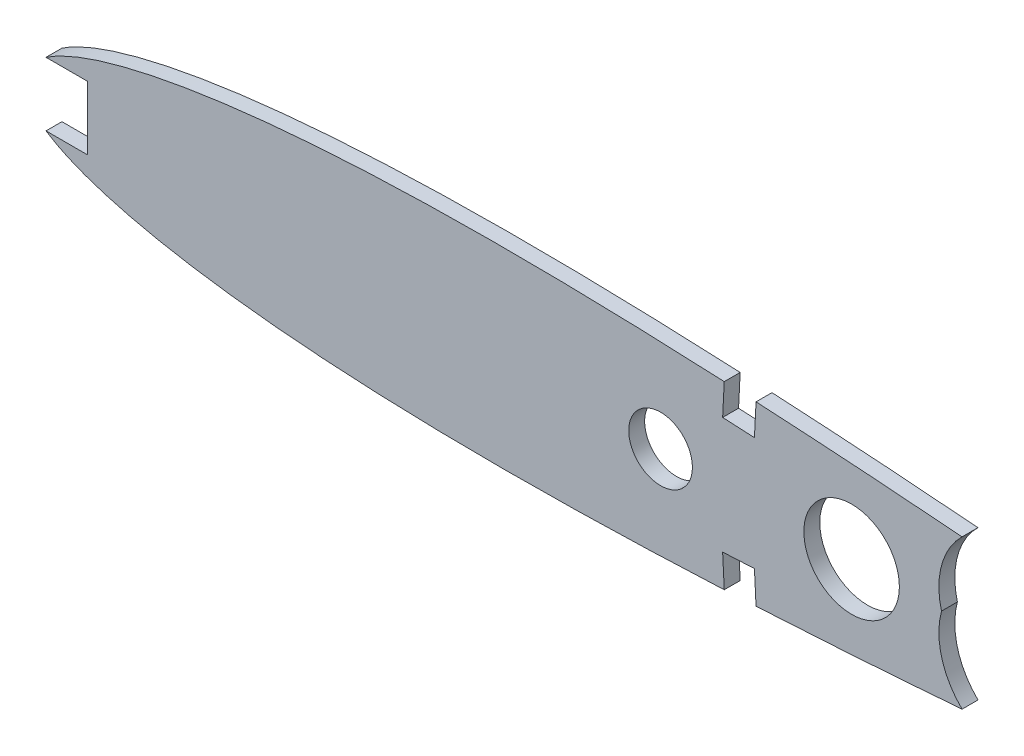
SolidWorks part; units mm, degrees
material "Plywood"
ref_plane "Front Plane" through (0, 0, 0) normal (0, 0, 1) x (1, 0, 0)
ref_plane "Top Plane" through (0, 0, 0) normal (0, 1, 0) x (1, 0, 0)
ref_plane "Right Plane" through (0, 0, 0) normal (1, 0, 0) x (0, 0, -1)
curve "Curve1"
  spline degree 3 poles (318.9616, -0.5388, 0) (318.9616, 0.5388, 0) (317.8871, 0.4072, 0) (316.5257, 0.7904, 0) (314.029, 1.0273, 0) (310.6656, 1.5357, 0) (306.333, 2.103, 0) (301.1081, 2.8022, 0) (295.0047, 3.5926, 0) (288.0667, 4.4725, 0) (280.3349, 5.4267, 0) (271.8575, 6.4421, 0) (262.6867, 7.5062, 0) (252.8789, 8.6045, 0) (242.4947, 9.7236, 0) (231.5982, 10.8496, 0) (220.2564, 11.9679, 0) (208.5394, 13.0629, 0) (196.5193, 14.1202, 0) (184.2704, 15.122, 0) (171.8679, 16.0521, 0) (159.3884, 16.8933, 0) (146.9087, 17.6278, 0) (134.5058, 18.2372, 0) (122.2562, 18.7052, 0) (110.2351, 19.0165, 0) (98.5168, 19.156, 0) (87.1732, 19.1125, 0) (76.2743, 18.8777, 0) (65.8873, 18.4456, 0) (56.076, 17.8151, 0) (46.9007, 16.9881, 0) (38.4176, 15.971, 0) (30.6784, 14.7725, 0) (23.73, 13.4051, 0) (17.6131, 11.8842, 0) (12.3624, 10.2248, 0) (8.0047, 8.4423, 0) (4.5539, 6.5486, 0) (2.0152, 4.5401, 0) (0.3892, 2.3682, 0) (-0.1814, 0, 0) (0.3892, -2.3682, 0) (2.0152, -4.5401, 0) (4.5539, -6.5486, 0) (8.0047, -8.4423, 0) (12.3624, -10.2248, 0) (17.6131, -11.8842, 0) (23.73, -13.4051, 0) (30.6784, -14.7725, 0) (38.4176, -15.971, 0) (46.9007, -16.9881, 0) (56.076, -17.8151, 0) (65.8873, -18.4456, 0) (76.2743, -18.8777, 0) (87.1732, -19.1125, 0) (98.5168, -19.156, 0) (110.2351, -19.0165, 0) (122.2562, -18.7052, 0) (134.5058, -18.2372, 0) (146.9087, -17.6278, 0) (159.3884, -16.8933, 0) (171.8679, -16.0521, 0) (184.2704, -15.122, 0) (196.5193, -14.1202, 0) (208.5394, -13.0629, 0) (220.2564, -11.9679, 0) (231.5982, -10.8496, 0) (242.4947, -9.7236, 0) (252.8789, -8.6045, 0) (262.6867, -7.5062, 0) (271.8575, -6.4421, 0) (280.3349, -5.4267, 0) (288.0667, -4.4725, 0) (295.0047, -3.5926, 0) (301.1081, -2.8022, 0) (306.333, -2.103, 0) (310.6656, -1.5357, 0) (314.029, -1.0273, 0) (316.5257, -0.7904, 0) (317.8871, -0.4072, 0) (318.9616, -0.5388, 0) (318.9616, 0.5388, 0) (317.8871, 0.4072, 0) knots -0.004279 -0.001997 -0.001234 0 0.000762 0.003045 0.006832 0.012101 0.018818 0.026939 0.036415 0.047185 0.05918 0.072328 0.086544 0.101741 0.117823 0.134691 0.15224 0.170361 0.188941 0.207865 0.227016 0.246276 0.265525 0.284645 0.30352 0.322035 0.340078 0.357543 0.374325 0.39033 0.405464 0.419644 0.432793 0.444844 0.455738 0.465429 0.473886 0.481102 0.487102 0.491975 0.495931 0.499383 0.502835 0.50679 0.511664 0.517664 0.524879 0.533337 0.543028 0.553922 0.565972 0.579122 0.593302 0.608436 0.62444 0.641223 0.658687 0.676731 0.695245 0.714121 0.733241 0.75249 0.77175 0.7909 0.809825 0.828404 0.846525 0.864074 0.880942 0.897025 0.912222 0.926438 0.939585 0.951581 0.962351 0.971826 0.979948 0.986664 0.991933 0.995721 0.998003 0.998766 1 1.000762 1.003045 1.006832 periodic
sketch "Sketch2" plane through (0, 0, 0) normal (0, 0, 1) x (1, 0, 0)
  spline S0 degree 3 poles (318.9616, -0.5388) (318.9616, 0.5388) (317.8871, 0.4072) (316.5257, 0.7904) (314.029, 1.0273) (310.6656, 1.5357) (306.333, 2.103) (301.1081, 2.8022) (295.0047, 3.5926) (288.0667, 4.4725) (280.3349, 5.4267) (271.8575, 6.4421) (262.6867, 7.5062) (252.8789, 8.6045) (242.4947, 9.7236) (231.5982, 10.8496) (220.2564, 11.9679) (208.5394, 13.0629) (196.5193, 14.1202) (184.2704, 15.122) (171.8679, 16.0521) (159.3884, 16.8933) (146.9087, 17.6278) (134.5058, 18.2372) (122.2562, 18.7052) (110.2351, 19.0165) (98.5168, 19.156) (87.1732, 19.1125) (76.2743, 18.8777) (65.8873, 18.4456) (56.076, 17.8151) (46.9007, 16.9881) (38.4176, 15.971) (30.6784, 14.7725) (23.73, 13.4051) (17.6131, 11.8842) (12.3624, 10.2248) (8.0047, 8.4423) (4.5539, 6.5486) (2.0152, 4.5401) (0.3892, 2.3682) (-0.1814, 0) (0.3892, -2.3682) (2.0152, -4.5401) (4.5539, -6.5486) (8.0047, -8.4423) (12.3624, -10.2248) (17.6131, -11.8842) (23.73, -13.4051) (30.6784, -14.7725) (38.4176, -15.971) (46.9007, -16.9881) (56.076, -17.8151) (65.8873, -18.4456) (76.2743, -18.8777) (87.1732, -19.1125) (98.5168, -19.156) (110.2351, -19.0165) (122.2562, -18.7052) (134.5058, -18.2372) (146.9087, -17.6278) (159.3884, -16.8933) (171.8679, -16.0521) (184.2704, -15.122) (196.5193, -14.1202) (208.5394, -13.0629) (220.2564, -11.9679) (231.5982, -10.8496) (242.4947, -9.7236) (252.8789, -8.6045) (262.6867, -7.5062) (271.8575, -6.4421) (280.3349, -5.4267) (288.0667, -4.4725) (295.0047, -3.5926) (301.1081, -2.8022) (306.333, -2.103) (310.6656, -1.5357) (314.029, -1.0273) (316.5257, -0.7904) (317.8871, -0.4072) (318.9616, -0.5388) (318.9616, 0.5388) (317.8871, 0.4072) knots -0.004279 -0.001997 -0.001234 0 0.000762 0.003045 0.006832 0.012101 0.018818 0.026939 0.036415 0.047185 0.05918 0.072328 0.086544 0.101741 0.117823 0.134691 0.15224 0.170361 0.188941 0.207865 0.227016 0.246276 0.265525 0.284645 0.30352 0.322035 0.340078 0.357543 0.374325 0.39033 0.405464 0.419644 0.432793 0.444844 0.455738 0.465429 0.473886 0.481102 0.487102 0.491975 0.495931 0.499383 0.502835 0.50679 0.511664 0.517664 0.524879 0.533337 0.543028 0.553922 0.565972 0.579122 0.593302 0.608436 0.62444 0.641223 0.658687 0.676731 0.695245 0.714121 0.733241 0.75249 0.77175 0.7909 0.809825 0.828404 0.846525 0.864074 0.880942 0.897025 0.912222 0.926438 0.939585 0.951581 0.962351 0.971826 0.979948 0.986664 0.991933 0.995721 0.998003 0.998766 1 1.000762 1.003045 1.006832 only from (318.77, 0.4017) to (318.77, 0.4017) construction
  spline S1 degree 3 poles (318.9616, -0.5388) (318.9616, 0.5388) (317.8871, 0.4072) (316.5257, 0.7904) (314.029, 1.0273) (310.6656, 1.5357) (306.333, 2.103) (301.1081, 2.8022) (295.0047, 3.5926) (288.0667, 4.4725) (280.3349, 5.4267) (271.8575, 6.4421) (262.6867, 7.5062) (252.8789, 8.6045) (242.4947, 9.7236) (231.5982, 10.8496) (220.2564, 11.9679) (208.5394, 13.0629) (196.5193, 14.1202) (184.2704, 15.122) (171.8679, 16.0521) (159.3884, 16.8933) (146.9087, 17.6278) (134.5058, 18.2372) (122.2562, 18.7052) (110.2351, 19.0165) (98.5168, 19.156) (87.1732, 19.1125) (76.2743, 18.8777) (65.8873, 18.4456) (56.076, 17.8151) (46.9007, 16.9881) (38.4176, 15.971) (30.6784, 14.7725) (23.73, 13.4051) (17.6131, 11.8842) (12.3624, 10.2248) (8.0047, 8.4423) (4.5539, 6.5486) (2.0152, 4.5401) (0.3892, 2.3682) (-0.1814, 0) (0.3892, -2.3682) (2.0152, -4.5401) (4.5539, -6.5486) (8.0047, -8.4423) (12.3624, -10.2248) (17.6131, -11.8842) (23.73, -13.4051) (30.6784, -14.7725) (38.4176, -15.971) (46.9007, -16.9881) (56.076, -17.8151) (65.8873, -18.4456) (76.2743, -18.8777) (87.1732, -19.1125) (98.5168, -19.156) (110.2351, -19.0165) (122.2562, -18.7052) (134.5058, -18.2372) (146.9087, -17.6278) (159.3884, -16.8933) (171.8679, -16.0521) (184.2704, -15.122) (196.5193, -14.1202) (208.5394, -13.0629) (220.2564, -11.9679) (231.5982, -10.8496) (242.4947, -9.7236) (252.8789, -8.6045) (262.6867, -7.5062) (271.8575, -6.4421) (280.3349, -5.4267) (288.0667, -4.4725) (295.0047, -3.5926) (301.1081, -2.8022) (306.333, -2.103) (310.6656, -1.5357) (314.029, -1.0273) (316.5257, -0.7904) (317.8871, -0.4072) (318.9616, -0.5388) (318.9616, 0.5388) (317.8871, 0.4072) knots -0.004279 -0.001997 -0.001234 0 0.000762 0.003045 0.006832 0.012101 0.018818 0.026939 0.036415 0.047185 0.05918 0.072328 0.086544 0.101741 0.117823 0.134691 0.15224 0.170361 0.188941 0.207865 0.227016 0.246276 0.265525 0.284645 0.30352 0.322035 0.340078 0.357543 0.374325 0.39033 0.405464 0.419644 0.432793 0.444844 0.455738 0.465429 0.473886 0.481102 0.487102 0.491975 0.495931 0.499383 0.502835 0.50679 0.511664 0.517664 0.524879 0.533337 0.543028 0.553922 0.565972 0.579122 0.593302 0.608436 0.62444 0.641223 0.658687 0.676731 0.695245 0.714121 0.733241 0.75249 0.77175 0.7909 0.809825 0.828404 0.846525 0.864074 0.880942 0.897025 0.912222 0.926438 0.939585 0.951581 0.962351 0.971826 0.979948 0.986664 0.991933 0.995721 0.998003 0.998766 1 1.000762 1.003045 1.006832 only from (318.77, 0.4017) to (318.77, 0.4017)
extrude "Boss-Extrude1" add sketch "Sketch2" along normal blind 3.175
sketch "Sketch3" plane through (0, 0, 3.175) normal (0, 0, 1) x (1, 0, 0)
  line L5 (146.0418, 17.6541) -> (145.7194, 11.3041)
  line L6 (139.7, 17.9761) -> (139.3776, 11.6261)
  line L7 (145.7194, 11.3041) -> (139.3776, 11.6261)
  line L8 (145.7194, -11.3041) -> (139.3776, -11.6261)
  line L9 (145.7194, -11.3041) -> (146.0418, -17.6541)
  line L10 (139.3776, -11.6261) -> (139.7, -17.9761)
  line L13 (139.7, 17.9761) -> (139.9721, 23.3363)
  line L14 (146.0418, 17.6541) -> (146.314, 23.0144)
  line L15 (139.9721, 23.3363) -> (146.314, 23.0144)
  line L17 (139.7, -17.9761) -> (139.8768, -21.459)
  line L18 (146.0418, -17.6541) -> (146.2187, -21.137)
  line L19 (139.8768, -21.459) -> (146.2187, -21.137)
  circle A1 centre (127, 0) radius 6.35
  spline S0 degree 3 poles (318.9616, -0.5388) (318.9616, 0.5388) (317.8871, 0.4072) (316.5257, 0.7904) (314.029, 1.0273) (310.6656, 1.5357) (306.333, 2.103) (301.1081, 2.8022) (295.0047, 3.5926) (288.0667, 4.4725) (280.3349, 5.4267) (271.8575, 6.4421) (262.6867, 7.5062) (252.8789, 8.6045) (242.4947, 9.7236) (231.5982, 10.8496) (220.2564, 11.9679) (208.5394, 13.0629) (196.5193, 14.1202) (184.2704, 15.122) (171.8679, 16.0521) (159.3884, 16.8933) (146.9087, 17.6278) (134.5058, 18.2372) (122.2562, 18.7052) (110.2351, 19.0165) (98.5168, 19.156) (87.1732, 19.1125) (76.2743, 18.8777) (65.8873, 18.4456) (56.076, 17.8151) (46.9007, 16.9881) (38.4176, 15.971) (30.6784, 14.7725) (23.73, 13.4051) (17.6131, 11.8842) (12.3624, 10.2248) (8.0047, 8.4423) (4.5539, 6.5486) (2.0152, 4.5401) (0.3892, 2.3682) (-0.1814, 0) (0.3892, -2.3682) (2.0152, -4.5401) (4.5539, -6.5486) (8.0047, -8.4423) (12.3624, -10.2248) (17.6131, -11.8842) (23.73, -13.4051) (30.6784, -14.7725) (38.4176, -15.971) (46.9007, -16.9881) (56.076, -17.8151) (65.8873, -18.4456) (76.2743, -18.8777) (87.1732, -19.1125) (98.5168, -19.156) (110.2351, -19.0165) (122.2562, -18.7052) (134.5058, -18.2372) (146.9087, -17.6278) (159.3884, -16.8933) (171.8679, -16.0521) (184.2704, -15.122) (196.5193, -14.1202) (208.5394, -13.0629) (220.2564, -11.9679) (231.5982, -10.8496) (242.4947, -9.7236) (252.8789, -8.6045) (262.6867, -7.5062) (271.8575, -6.4421) (280.3349, -5.4267) (288.0667, -4.4725) (295.0047, -3.5926) (301.1081, -2.8022) (306.333, -2.103) (310.6656, -1.5357) (314.029, -1.0273) (316.5257, -0.7904) (317.8871, -0.4072) (318.9616, -0.5388) (318.9616, 0.5388) (317.8871, 0.4072) knots -0.004279 -0.001997 -0.001234 0 0.000762 0.003045 0.006832 0.012101 0.018818 0.026939 0.036415 0.047185 0.05918 0.072328 0.086544 0.101741 0.117823 0.134691 0.15224 0.170361 0.188941 0.207865 0.227016 0.246276 0.265525 0.284645 0.30352 0.322035 0.340078 0.357543 0.374325 0.39033 0.405464 0.419644 0.432793 0.444844 0.455738 0.465429 0.473886 0.481102 0.487102 0.491975 0.495931 0.499383 0.502835 0.50679 0.511664 0.517664 0.524879 0.533337 0.543028 0.553922 0.565972 0.579122 0.593302 0.608436 0.62444 0.641223 0.658687 0.676731 0.695245 0.714121 0.733241 0.75249 0.77175 0.7909 0.809825 0.828404 0.846525 0.864074 0.880942 0.897025 0.912222 0.926438 0.939585 0.951581 0.962351 0.971826 0.979948 0.986664 0.991933 0.995721 0.998003 0.998766 1 1.000762 1.003045 1.006832 only from (318.77, 0.4017) to (318.77, 0.4017) construction
  dimension "D1" = 6.35
  dimension "D2" = 12.7
  dimension "D3" = 6.35
  dimension "D4" = 127
  dimension "D5" = 12.7
  dimension "D6" = 0
  dimension "D7" = 6.35
  dimension "D8" = 6.35
extrude "Cut-Extrude1" cut sketch "Sketch3" against normal through all
sketch "Sketch4" plane through (0, 0, 3.175) normal (0, 0, 1) x (1, 0, 0)
  line L5 (12.7, 6.35) -> (12.7, -6.35)
  line L6 (12.7, 6.35) -> (0, 6.35)
  line L7 (12.7, -6.35) -> (0, -6.35)
  line L8 (0, 6.35) -> (0, -6.35)
  line L9 (12.7, 6.35) -> (0, -6.35) construction
  line L10 (12.7, -6.35) -> (0, 6.35) construction
  spline S0 degree 3 poles (318.9616, -0.5388) (318.9616, 0.5388) (317.8871, 0.4072) (316.5257, 0.7904) (314.029, 1.0273) (310.6656, 1.5357) (306.333, 2.103) (301.1081, 2.8022) (295.0047, 3.5926) (288.0667, 4.4725) (280.3349, 5.4267) (271.8575, 6.4421) (262.6867, 7.5062) (252.8789, 8.6045) (242.4947, 9.7236) (231.5982, 10.8496) (220.2564, 11.9679) (208.5394, 13.0629) (196.5193, 14.1202) (184.2704, 15.122) (171.8679, 16.0521) (159.3884, 16.8933) (146.9087, 17.6278) (134.5058, 18.2372) (122.2562, 18.7052) (110.2351, 19.0165) (98.5168, 19.156) (87.1732, 19.1125) (76.2743, 18.8777) (65.8873, 18.4456) (56.076, 17.8151) (46.9007, 16.9881) (38.4176, 15.971) (30.6784, 14.7725) (23.73, 13.4051) (17.6131, 11.8842) (12.3624, 10.2248) (8.0047, 8.4423) (4.5539, 6.5486) (2.0152, 4.5401) (0.3892, 2.3682) (-0.1814, 0) (0.3892, -2.3682) (2.0152, -4.5401) (4.5539, -6.5486) (8.0047, -8.4423) (12.3624, -10.2248) (17.6131, -11.8842) (23.73, -13.4051) (30.6784, -14.7725) (38.4176, -15.971) (46.9007, -16.9881) (56.076, -17.8151) (65.8873, -18.4456) (76.2743, -18.8777) (87.1732, -19.1125) (98.5168, -19.156) (110.2351, -19.0165) (122.2562, -18.7052) (134.5058, -18.2372) (146.9087, -17.6278) (159.3884, -16.8933) (171.8679, -16.0521) (184.2704, -15.122) (196.5193, -14.1202) (208.5394, -13.0629) (220.2564, -11.9679) (231.5982, -10.8496) (242.4947, -9.7236) (252.8789, -8.6045) (262.6867, -7.5062) (271.8575, -6.4421) (280.3349, -5.4267) (288.0667, -4.4725) (295.0047, -3.5926) (301.1081, -2.8022) (306.333, -2.103) (310.6656, -1.5357) (314.029, -1.0273) (316.5257, -0.7904) (317.8871, -0.4072) (318.9616, -0.5388) (318.9616, 0.5388) (317.8871, 0.4072) knots -0.004279 -0.001997 -0.001234 0 0.000762 0.003045 0.006832 0.012101 0.018818 0.026939 0.036415 0.047185 0.05918 0.072328 0.086544 0.101741 0.117823 0.134691 0.15224 0.170361 0.188941 0.207865 0.227016 0.246276 0.265525 0.284645 0.30352 0.322035 0.340078 0.357543 0.374325 0.39033 0.405464 0.419644 0.432793 0.444844 0.455738 0.465429 0.473886 0.481102 0.487102 0.491975 0.495931 0.499383 0.502835 0.50679 0.511664 0.517664 0.524879 0.533337 0.543028 0.553922 0.565972 0.579122 0.593302 0.608436 0.62444 0.641223 0.658687 0.676731 0.695245 0.714121 0.733241 0.75249 0.77175 0.7909 0.809825 0.828404 0.846525 0.864074 0.880942 0.897025 0.912222 0.926438 0.939585 0.951581 0.962351 0.971826 0.979948 0.986664 0.991933 0.995721 0.998003 0.998766 1 1.000762 1.003045 1.006832 only from (318.77, 0.4017) to (318.77, 0.4017) construction
  spline S1 degree 3 poles (44.4469, 16.6766) (42.3575, 16.4398) (37.6765, 15.8562) (30.6784, 14.7725) (23.73, 13.4051) (17.6131, 11.8842) (12.3624, 10.2248) (8.0047, 8.4423) (4.5539, 6.5486) (2.0152, 4.5401) (0.3892, 2.3682) (-0.1814, 0) (0.3892, -2.3682) (2.0152, -4.5401) (4.5539, -6.5486) (8.0047, -8.4423) (12.3624, -10.2248) (17.6131, -11.8842) (23.73, -13.4051) (30.6784, -14.7725) (37.6765, -15.8562) (42.3575, -16.4398) (44.4469, -16.6766) knots 0.4231 0.4231 0.4231 0.4231 0.432793 0.444844 0.455738 0.465429 0.473886 0.481102 0.487102 0.491975 0.495931 0.499383 0.502835 0.50679 0.511664 0.517664 0.524879 0.533337 0.543028 0.553922 0.565972 0.575665 0.575665 0.575665 0.575665
  point P4 (6.35, 0)
  dimension "D2" = 12.7
  dimension "D1" = 12.7
  dimension "D3" = 6.35
extrude "Cut-Extrude2" cut sketch "Sketch4" against normal through all contours L5 L7 L8 L6
sketch "Sketch5" plane through (0, 0, 3.175) normal (0, 0, 1) x (1, 0, 0)
  line L0 (1.7463, 0) -> (-1.7463, 0) construction
  line L1 (183.0237, 0) -> (228.7437, 0) construction
  line L4 (183.0237, 0) -> (202.931, 5.3341) construction
  line L5 (183.0237, 0) -> (200.3978, -4.6554) construction
  line L6 (188.7633, 17.0935) -> (187.3498, 15.0894)
  line L7 (188.589, -18.0751) -> (187.2309, -14.9772)
  arc A1 (187.3498, 15.0894) -> (183.0237, 0) centre (197.7444, 3.9444) ccw
  arc A2 (183.0237, 0) -> (187.2309, -14.9772) centre (197.7444, -3.9444) ccw
  spline S1 degree 3 poles (188.589, -18.0751) (191.8244, -17.8303) (199.8411, -17.2062) (212.5165, -16.1546) (226.4666, -14.9207) (239.9702, -13.6568) (252.9441, -12.3811) (265.3082, -11.1106) (276.9862, -9.8615) (287.906, -8.6493) (298.0004, -7.4909) (307.2071, -6.401) (315.4687, -5.3948) (322.7367, -4.4902) (328.9585, -3.689) (334.1178, -3.0394) (338.1234, -2.4543) (341.0959, -2.1871) (342.7183, -1.7391) (343.9962, -1.902) (344.0026, -0.6197) (342.7231, -0.7699) (341.1052, -0.3058) (338.1355, -0.0092) (334.1359, 0.6156) (328.9833, 1.3163) (322.7697, 2.1792) (315.5111, 3.1557) (307.2599, 4.2439) (298.0644, 5.425) (287.982, 6.6834) (277.0748, 8.0038) (265.4097, 9.3687) (253.0588, 10.7617) (240.0982, 12.1659) (226.6078, 13.5637) (212.6706, 14.9359) (200.0063, 16.1131) (191.9961, 16.8166) (188.7633, 17.0935) knots 0.797256 0.797256 0.797256 0.797256 0.809825 0.828404 0.846525 0.864074 0.880942 0.897025 0.912222 0.926438 0.939585 0.951581 0.962351 0.971826 0.979948 0.986664 0.991933 0.995721 0.998003 0.998766 1 1.000762 1.003045 1.006832 1.012101 1.018818 1.026939 1.036415 1.047185 1.05918 1.072328 1.086544 1.101741 1.117823 1.134691 1.15224 1.170361 1.188941 1.20151 1.20151 1.20151 1.20151
  point P0 (318.9137, 0)
  dimension "D5" = 30.48
  dimension "D6" = 30.48
  dimension "D1" = 135.89
  dimension "D3" = 15
  dimension "D4" = 15
extrude "Cut-Extrude3" cut sketch "Sketch5" against normal through all
sketch "Sketch9" plane through (0, 0, 3.175) normal (0, 0, 1) x (1, 0, 0)
  circle A0 centre (165.1, 0) radius 9.525
  dimension "D1" = 19.05
  dimension "D2" = 165.1
extrude "Cut-Extrude5" cut sketch "Sketch9" against normal blind 5.08
sketch "Sketch8" [suppressed] plane through (0, 0, 3.175) normal (0, 0, 1) x (1, 0, 0)
  line L0 (60.96, -6.35) -> (72.0725, -6.35)
  line L1 (60.96, 9.525) -> (86.36, 9.525)
  line L2 (60.96, 9.525) -> (60.96, 6.35)
  line L3 (60.96, 6.35) -> (72.0725, 6.35)
  line L4 (86.36, 9.525) -> (86.36, 6.35)
  line L5 (60.96, -6.35) -> (60.96, -9.525)
  line L6 (60.96, -9.525) -> (86.36, -9.525)
  line L7 (86.36, -6.35) -> (86.36, -9.525)
  line L8 (75.2475, 6.35) -> (86.36, 6.35)
  line L10 (72.0725, 6.35) -> (72.0725, -6.35)
  line L12 (75.2475, 6.35) -> (75.2475, -6.35)
  line L13 (75.2475, -6.35) -> (86.36, -6.35)
  dimension "D1" = 3.175
  dimension "D2" = 25.4
  dimension "D3" = 3.175
  dimension "D4" = 25.4
  dimension "D5" = 12.7
  dimension "D6" = 3.175
  dimension "D7" = 11.1125
  dimension "D8" = 6.35
  dimension "D9" = 60.96
extrude "Cut-Extrude6" [suppressed] cut sketch "Sketch8" against normal blind 5.08
